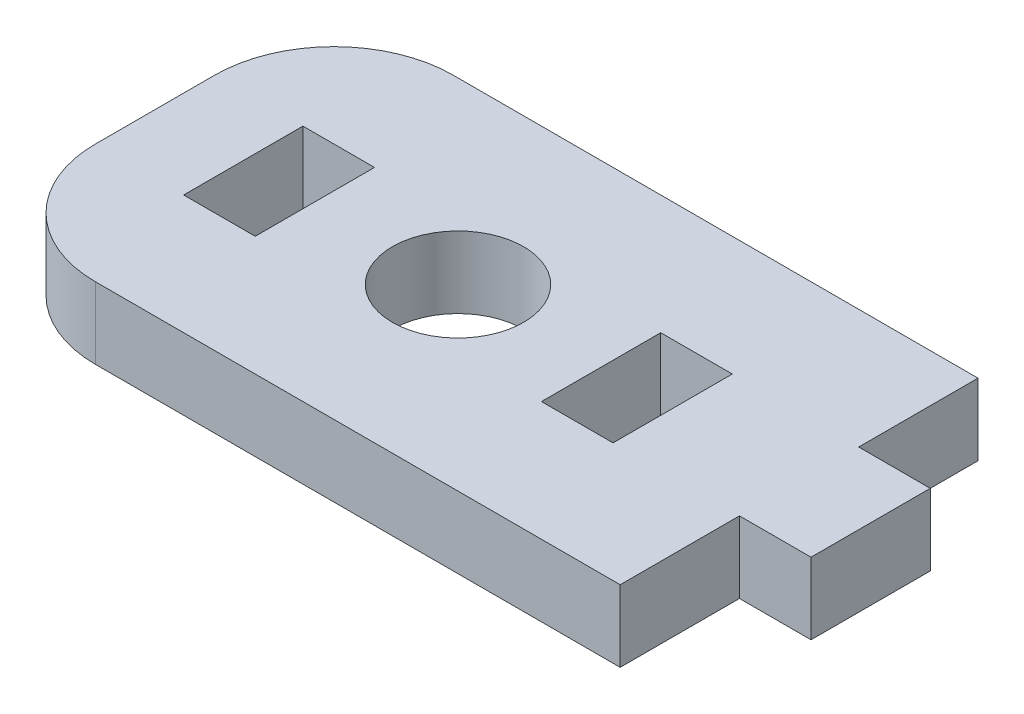
SolidWorks part; units mm, degrees
ref_plane "Front Plane" through (0, 0, 0) normal (0, 0, 1) x (1, 0, 0)
ref_plane "Top Plane" through (0, 0, 0) normal (0, 1, 0) x (1, 0, 0)
ref_plane "Right Plane" through (0, 0, 0) normal (1, 0, 0) x (0, 0, -1)
sketch "Sketch1" plane through (0, 0, 0) normal (0, 1, 0) x (1, 0, 0)
  line L0 (-21.8216, -5) -> (-21.8216, 10)
  line L1 (-21.8216, 10) -> (5.1784, 10)
  line L2 (5.1784, 10) -> (5.1784, 5)
  line L3 (5.1784, 5) -> (8.1784, 5)
  line L4 (8.1784, 5) -> (8.1784, 0)
  line L5 (8.1784, 0) -> (5.1784, 0)
  line L6 (5.1784, 0) -> (5.1784, -5)
  line L7 (5.1784, -5) -> (-21.8216, -5)
  line L8 (-21.8216, 2.5) -> (-16.6216, 2.5) construction
  line L9 (-16.6216, 2.5) -> (-9.1216, 2.5) construction
  line L10 (-15.1216, 5) -> (-18.1216, 5)
  line L11 (-15.1216, 5) -> (-15.1216, 0)
  line L12 (-15.1216, 0) -> (-18.1216, 0)
  line L13 (-18.1216, 5) -> (-18.1216, 0)
  line L14 (-15.1216, 5) -> (-18.1216, 0) construction
  line L15 (-15.1216, 0) -> (-18.1216, 5) construction
  line L16 (-9.1216, 2.5) -> (-9.1216, 50002.5) construction
  line L17 (-3.1216, 0) -> (-0.1216, 5) construction
  line L18 (-3.1216, 5) -> (-0.1216, 0) construction
  line L19 (-0.1216, 5) -> (-0.1216, 0)
  line L20 (-3.1216, 0) -> (-0.1216, 0)
  line L21 (-3.1216, 5) -> (-3.1216, 0)
  line L22 (-3.1216, 5) -> (-0.1216, 5)
  circle A0 centre (-9.1216, 2.5) radius 2.75
  dimension "D8" = 5.5
  dimension "D1" = 3
  dimension "D2" = 5
  dimension "D3" = 5
  dimension "D4" = 27
  dimension "D5" = 5.2
  dimension "D6" = 3
  dimension "D7" = 5
  dimension "D9" = 7.5
extrude "Boss-Extrude1" add sketch "Sketch1" along normal blind 3
fillet "Fillet1" radius 5 2 edges at (-21.8216, 1.5, 5) (-21.8216, 1.5, -10)
